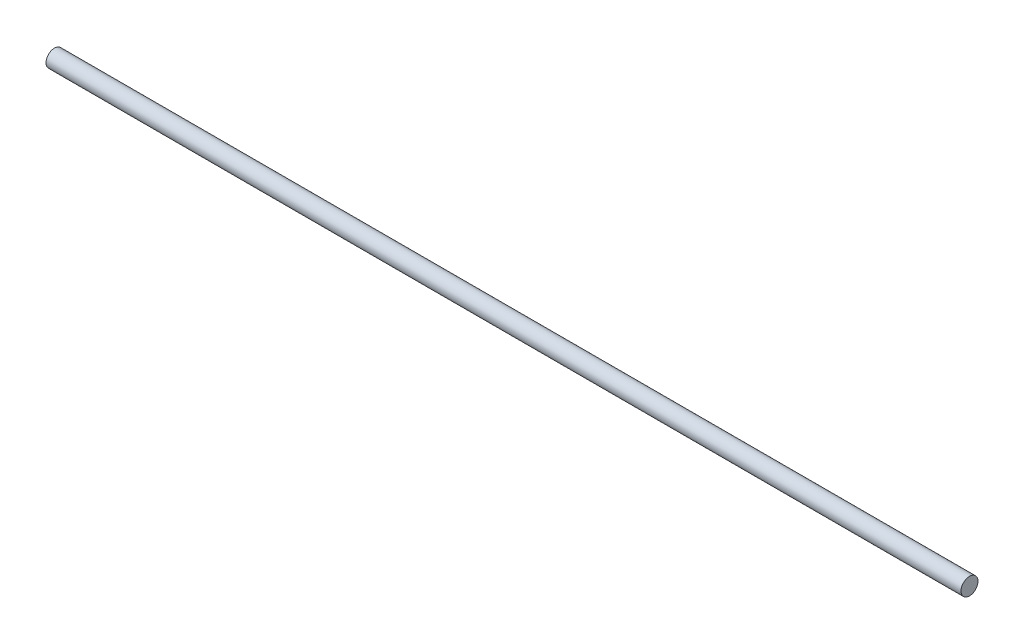
SolidWorks part; units mm, degrees
ref_plane "Front Plane" through (0, 0, 0) normal (0, 0, 1) x (1, 0, 0)
ref_plane "Top Plane" through (0, 0, 0) normal (0, 1, 0) x (1, 0, 0)
ref_plane "Right Plane" through (0, 0, 0) normal (1, 0, 0) x (0, 0, -1)
sketch "Sketch1" plane through (0, 0, 0) normal (1, 0, 0) x (0, 0, -1)
  circle A0 centre (0, 0) radius 6.35
  dimension "D1" = 12.7
extrude "Boss-Extrude1" add sketch "Sketch1" along normal blind 683.514
cosmetic thread "Cosmetic Thread1"
equation "\"glass pane length\" = 14.09375"
equation "\"glass pane width\" = 10.15625"
equation "\"glass pane wall width\" = 3/4"
equation "\"glass lip\" = 1/4"
equation "\"bolt diameter\" = 0.2"
equation "\"stepper body width\" = 2.22"
equation "\"stepper mount offset\" = 0.19"
equation "\"stepper mount diameter\" = 0.19"
equation "\"stepper spacer thickness\" = 0.2"
equation "\"y axis stepper wall height off base\" = 8"
equation "\"y axis stepper wall bracket thickness\" = 1"
equation "\"y axis stepper wall mount side offset\" = 1/2"
equation "\"y axis stepper wall mount top offset\" = 1/2"
equation "\"y axis stepper wall width\" = \"stepper body width\" + 1"
equation "\"thin metal\" = 0.12"
equation "\"thick metal\" = 0.25"
equation "\"stepper shaft offset from body\" = 0.79"
equation "\"base length\" = 27"
equation "\"base width\" = 20"
equation "\"y axis bracket height to hole\" = 3.5"
equation "\"foot diameter\" = 0.2"
equation "\"foot inset from corner\" = 1"
equation "\"recognizer width\" = 2.5"
equation "\"recognizer nut plate height\" = 1.25"
equation "\"recognizer nut plate offset\" = 1.5"
equation "\"recognizer arm length\" = 5"
equation "\"recognizer bracket length\" = 3"
